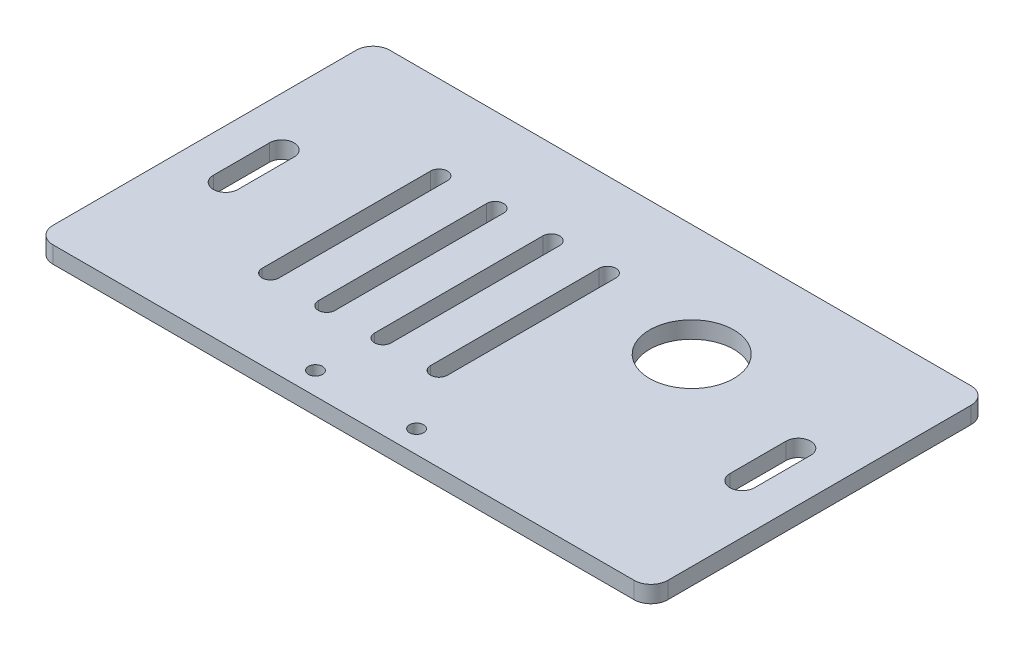
SolidWorks part; units mm, degrees
material "A-玻璃纤维"
ref_plane "前视基准面" through (0, 0, 0) normal (0, 0, 1) x (1, 0, 0)
ref_plane "上视基准面" through (0, 0, 0) normal (0, 1, 0) x (1, 0, 0)
ref_plane "右视基准面" through (0, 0, 0) normal (1, 0, 0) x (0, 0, -1)
sketch "草图1" plane through (0, 0, 0) normal (0, 1, 0) x (1, 0, 0)
  line L1 (-54.75, 30) -> (54.75, 30)
  line L2 (-54.75, 30) -> (-54.75, -30)
  line L3 (-54.75, -30) -> (54.75, -30)
  line L4 (54.75, 30) -> (54.75, -30)
  line L5 (-54.75, 30) -> (54.75, -30) construction
  line L6 (-54.75, -30) -> (54.75, 30) construction
  point P0 (0, 0)
  dimension "D1" = 109.5
  dimension "D2" = 60
extrude "凸台-拉伸1" add sketch "草图1" along normal blind 3
sketch "草图2" plane through (0, 3, 0) normal (0, 1, 0) x (1, 0, 0)
  line L0 (0, 0) -> (0, -30) construction
  line L1 (-54.75, -30) -> (54.75, -30) construction
  line L2 (-9, -26) -> (9, -26) construction
  circle A0 centre (9, -26) radius 1.25
  circle A1 centre (-9, -26) radius 1.25
  point P9 (0, -26)
  dimension "D2" = 2.5
  dimension "D1" = 9
  dimension "D3" = 4
extrude "切除-拉伸1" cut sketch "草图2" against normal blind 10
fillet "圆角1" radius 3 4 edges at (54.75, 1.5, 30) (-54.75, 1.5, -30) (54.75, 1.5, -30) (-54.75, 1.5, 30)
sketch "草图3" plane through (0, 3, 0) normal (0, 1, 0) x (1, 0, 0)
  line L0 (0, 0) -> (-46, 0) construction
  line L1 (0, 0) -> (0, 34.1011) construction
  line L2 (-46, 5) -> (-46, -5) construction
  line L3 (-43.8099, 5) -> (-43.8099, -5)
  line L4 (-48.1901, 5) -> (-48.1901, -5)
  line L5 (46, 5) -> (46, -5) construction
  line L6 (43.8099, 5) -> (43.8099, -5)
  line L7 (48.1901, 5) -> (48.1901, -5)
  arc A0 (-43.8099, 5) -> (-48.1901, 5) centre (-46, 5) ccw
  arc A1 (-48.1901, -5) -> (-43.8099, -5) centre (-46, -5) ccw
  arc A2 (43.8099, 5) -> (48.1901, 5) centre (46, 5) cw
  arc A3 (48.1901, -5) -> (43.8099, -5) centre (46, -5) cw
  point P6 (-46, 0)
  point P13 (46, 0)
  dimension "D1" = 2.1901
  dimension "D2" = 10
  dimension "D3" = 46
extrude "切除-拉伸2" cut sketch "草图3" against normal blind 10
sketch "草图5" plane through (0, 3, 0) normal (0, 1, 0) x (1, 0, 0)
  line L0 (0, 0) -> (0, 41.5698) construction
  line L1 (0, 0) -> (-28, 0) construction
  line L2 (-28, 15) -> (-28, -15) construction
  line L3 (-26.5, 15) -> (-26.5, -15)
  line L4 (-29.5, 15) -> (-29.5, -15)
  line L5 (-18, 15) -> (-18, -15) construction
  line L6 (-16.5, 15) -> (-16.5, -15)
  line L7 (-19.5, 15) -> (-19.5, -15)
  line L8 (-8, 15) -> (-8, -15) construction
  line L9 (-6.5, 15) -> (-6.5, -15)
  line L10 (-9.5, 15) -> (-9.5, -15)
  line L11 (2, 15) -> (2, -15) construction
  line L12 (3.5, 15) -> (3.5, -15)
  line L13 (0.5, 15) -> (0.5, -15)
  line L130 (12, 15) -> (12, -15) construction
  line L131 (13.5, 15) -> (13.5, -15)
  line L132 (10.5, 15) -> (10.5, -15)
  line L133 (22, 15) -> (22, -15) construction
  line L134 (23.5, 15) -> (23.5, -15)
  line L135 (20.5, 15) -> (20.5, -15)
  line L136 (32, 15) -> (32, -15) construction
  line L137 (33.5, 15) -> (33.5, -15)
  line L138 (30.5, 15) -> (30.5, -15)
  line L139 (12, 15) -> (12, -15) construction
  line L140 (13.5, 15) -> (13.5, -15)
  line L141 (10.5, 15) -> (10.5, -15)
  line L142 (22, 15) -> (22, -15) construction
  line L143 (23.5, 15) -> (23.5, -15)
  line L144 (20.5, 15) -> (20.5, -15)
  line L145 (32, 15) -> (32, -15) construction
  line L146 (33.5, 15) -> (33.5, -15)
  line L147 (30.5, 15) -> (30.5, -15)
  arc A1 (-26.5, 15) -> (-29.5, 15) centre (-28, 15) ccw
  arc A2 (-29.5, -15) -> (-26.5, -15) centre (-28, -15) ccw
  arc A3 (-16.5, 15) -> (-19.5, 15) centre (-18, 15) ccw
  arc A4 (-19.5, -15) -> (-16.5, -15) centre (-18, -15) ccw
  arc A5 (-6.5, 15) -> (-9.5, 15) centre (-8, 15) ccw
  arc A6 (-9.5, -15) -> (-6.5, -15) centre (-8, -15) ccw
  arc A7 (3.5, 15) -> (0.5, 15) centre (2, 15) ccw
  arc A8 (0.5, -15) -> (3.5, -15) centre (2, -15) ccw
  circle A15 centre (22, 10) radius 7.5
  arc A94 (13.5, 15) -> (10.5, 15) centre (12, 15) ccw
  arc A95 (10.5, -15) -> (13.5, -15) centre (12, -15) ccw
  arc A96 (23.5, 15) -> (20.5, 15) centre (22, 15) ccw
  arc A97 (20.5, -15) -> (23.5, -15) centre (22, -15) ccw
  arc A98 (33.5, 15) -> (30.5, 15) centre (32, 15) ccw
  arc A99 (30.5, -15) -> (33.5, -15) centre (32, -15) ccw
  point P6 (-28, 0)
  point P14 (-18, 0)
  point P21 (-8, 0)
  point P28 (2, 0)
  point P41 (15, 0)
  point P49 (16, 0)
  point P57 (26, 0)
  point P64 (16, 0)
  point P71 (26, 0)
  point P78 (20, 0)
  point P85 (30, 0)
  point P92 (20, 0)
  point P99 (30, 0)
  point P106 (20, 0)
  point P113 (30, 0)
  point P120 (20, 0)
  point P127 (30, 0)
  point P134 (25, 0)
  point P141 (35, 0)
  point P148 (25, 0)
  point P155 (35, 0)
  point P162 (25, 0)
  point P169 (35, 0)
  point P176 (15, 0)
  point P183 (25, 0)
  point P190 (35, 0)
  point P197 (15, 0)
  point P204 (25, 0)
  point P211 (35, 0)
  point P218 (15, 0)
  point P225 (25, 0)
  point P232 (35, 0)
  point P239 (12, 0)
  point P246 (22, 0)
  point P253 (32, 0)
  point P260 (12, 0)
  point P267 (22, 0)
  point P274 (32, 0)
  point P281 (12, 0)
  point P288 (22, 0)
  point P295 (32, 0)
  point P302 (12, 0)
  point P309 (22, 0)
  point P316 (32, 0)
  point P323 (12, 0)
  point P330 (22, 0)
  point P337 (32, 0)
  dimension "D1" = 1.5
  dimension "D6" = 15
  dimension "D7" = 10
  dimension "D8" = 22
  dimension "D2" = 30
  dimension "D3" = 28
  dimension "D5" = 10
  dimension "D4" = 7
extrude "切除-拉伸3" cut sketch "草图5" against normal blind 10
